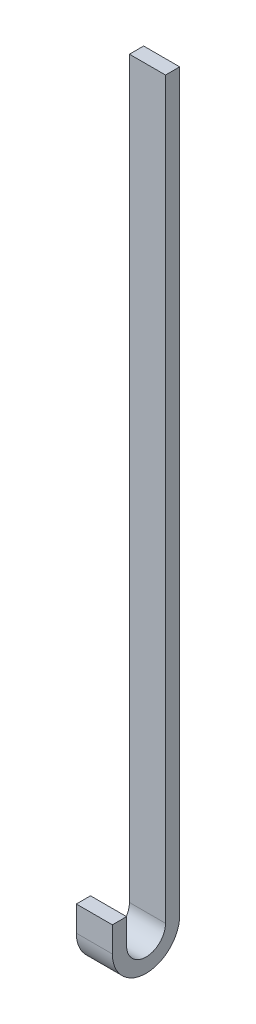
SolidWorks part; units mm, degrees
ref_plane "Front" through (0, 0, 0) normal (0, 0, 1) x (1, 0, 0)
ref_plane "Top" through (0, 0, 0) normal (0, 1, 0) x (1, 0, 0)
ref_plane "Right" through (0, 0, 0) normal (1, 0, 0) x (0, 0, -1)
sketch "Sketch1" plane through (0, 0, 0) normal (1, 0, 0) x (0, 0, -1)
  line L0 (0, 0) -> (0, -26.6925)
  line L1 (71.12, -26.6925) -> (71.12, 749.3)
  line L2 (14.986, 0) -> (14.986, -26.6925)
  line L3 (56.134, -26.6925) -> (56.134, 749.3)
  line L4 (0, 0) -> (14.986, 0)
  line L5 (56.134, 749.3) -> (71.12, 749.3)
  line L7 (146.7485, 723.9) -> (99.1235, 723.9) construction
  arc A0 (0, -26.6925) -> (71.12, -26.6925) centre (35.56, -26.6925) ccw
  arc A1 (14.986, -26.6925) -> (56.134, -26.6925) centre (35.56, -26.6925) ccw
  dimension "D1" = 914.4
  dimension "D2" = 71.12
  dimension "D4" = 41.148
  dimension "D5" = 25.4
  dimension "D3" = 14.986
extrude "Boss-Extrude1" add sketch "Sketch1" along normal blind 38.1
